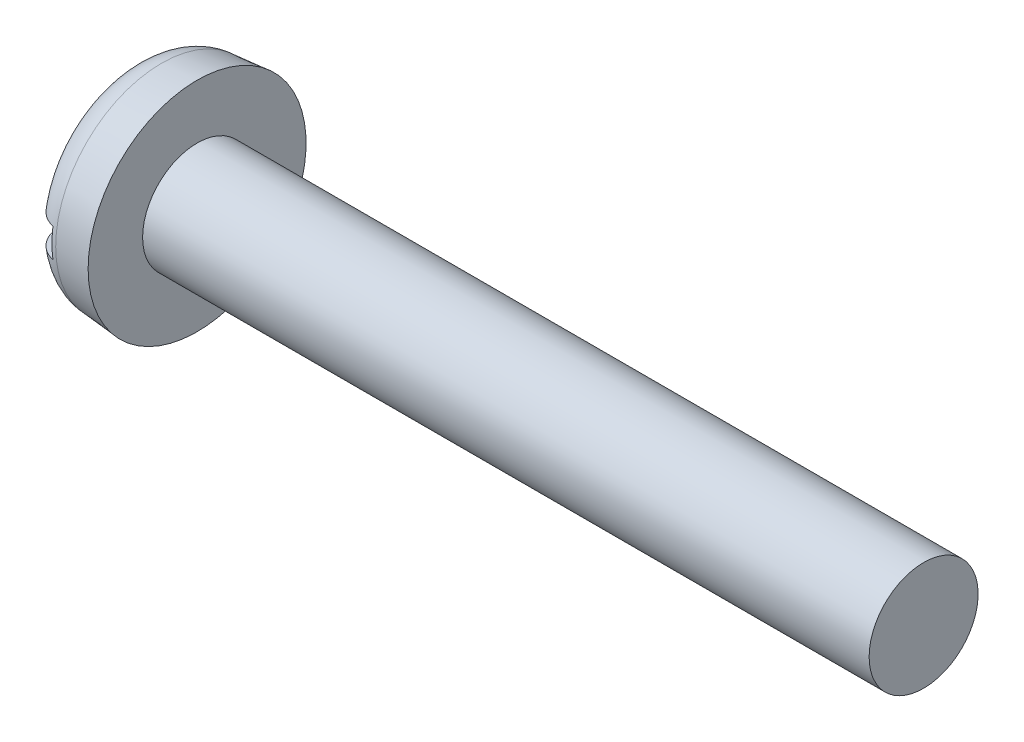
SolidWorks part; units mm, degrees
ref_plane "Plane1" through (0, 0, 0) normal (0, 0, 1) x (1, 0, 0)
ref_plane "Plane2" through (0, 0, 0) normal (0, 1, 0) x (1, 0, 0)
ref_plane "Plane3" through (0, 0, 0) normal (1, 0, 0) x (0, 0, -1)
sketch "BodySke" plane through (0, 0, 0) normal (0, 0, 1) x (1, 0, 0)
  line L0 (3.6, 3) -> (3.6, 6)
  line L1 (0, 0) -> (0, 5.685)
  line L2 (-25.4, 0) -> (127, 0) construction
  line L3 (43.6, 0) -> (0, 0)
  line L4 (3.6, 3) -> (43.6, 3)
  line L5 (43.6, 3) -> (43.6, 0)
  line L6 (0, 5.685) -> (3.6, 6)
  line L9 (4.6, 4.5875) -> (4.6, -4.9375) construction
  line L10 (3.6, 6.35) -> (3.6, -3.175) construction
  dimension "Length" = 40
  dimension "Thread_nom" = 40
  dimension "Head_side_angle" = 5
revolve "Base-Revolve" add sketch "BodySke"
cosmetic thread "ThreadCosmetic" [suppressed]
fillet "Fillet1" [suppressed] radius 0.25
fillet "Fillet2" radius 1.8 1 edges at (0, 0, 5.685)
sketch "Sketch2" plane through (0, 0, 0) normal (1, 0, 0) x (0, 0, -1)
  line L0 (6, -0.8) -> (-6, -0.8)
  line L1 (6, -0.8) -> (6, 0.8)
  line L2 (-6, 0.8) -> (6, 0.8)
  line L3 (-6, 0.8) -> (-6, -0.8)
  dimension "D1" = 9.5
  dimension "D2" = 4.75
  dimension "D3" = 0.6
extrude "Slot" cut sketch "Sketch2" along normal blind 1.4
sketch "ThdSchSke" plane through (0, 0, 0) normal (0, 0, 1) x (1, 0, 0)
  line L0 (5.6, -2.4455) -> (5.2117, -3)
  line L1 (5.6, -2.4455) -> (5.9883, -3)
  line L2 (5.9883, -3) -> (5.9883, -3.75)
  line L3 (-3.175, 0) -> (5.1513, 0) construction
  line L5 (5.9883, -3.75) -> (5.2117, -3.75)
  line L6 (5.2117, -3.75) -> (5.2117, -3)
  dimension "SideAngle" = 55
  dimension "VeeAngle" = 70
  dimension "Thread_minor" = 4.11
  dimension "Overcut" = 6.25
  dimension "Diameter" = 5
  dimension "Start" = 4.6
revolve "ThreadSchematic" [suppressed] cut sketch "ThdSchSke" angle 360 about L3
pattern_linear "ThdSchPat" [suppressed]
equation "\"D1@Sketch2\" = \"Head_dia@BodySke\""
equation "\"D2@Sketch2\" = \"D1@Sketch2\" / 2"
equation "\"D3@Sketch2\" = \"Slot_width@Sketch2\" / 2"
equation "\"Thread_length@ThreadCosmetic\" = ((sgn( (\"Length@BodySke\" - \"Advance@BodySke\" * 2.0 ) - \"Thread_nom@BodySke\" )-1)*( (\"Length@BodySke\" - \"Advance@BodySke\"  * 2.0) - \"Thread_nom@BodySke\" ))/-2+ \"Thread_nom@BodySke\""
equation "\"Thread_minor@ThdSchSke\" = \"Thread_minor@ThreadCosmetic\""
equation "\"Diameter@ThdSchSke\" = \"Diameter@BodySke\""
equation "\"Overcut@ThdSchSke\" = \"Diameter@BodySke\" * 1.25"
equation "\"Start@ThdSchSke\" = \"Head_ht@BodySke\" + \"Length@BodySke\" - \"Thread_length@ThreadCosmetic\"  '---Non-countersunk---"
equation "\"Num_threads@ThdSchPat\" = int( \"Thread_length@ThreadCosmetic\" / \"Advance@BodySke\" + 0.999 )  + 1"
equation "\"Advance@ThdSchPat\" = \"Thread_length@ThreadCosmetic\" /  (\"Num_threads@ThdSchPat\" - 1) 'relax it"
